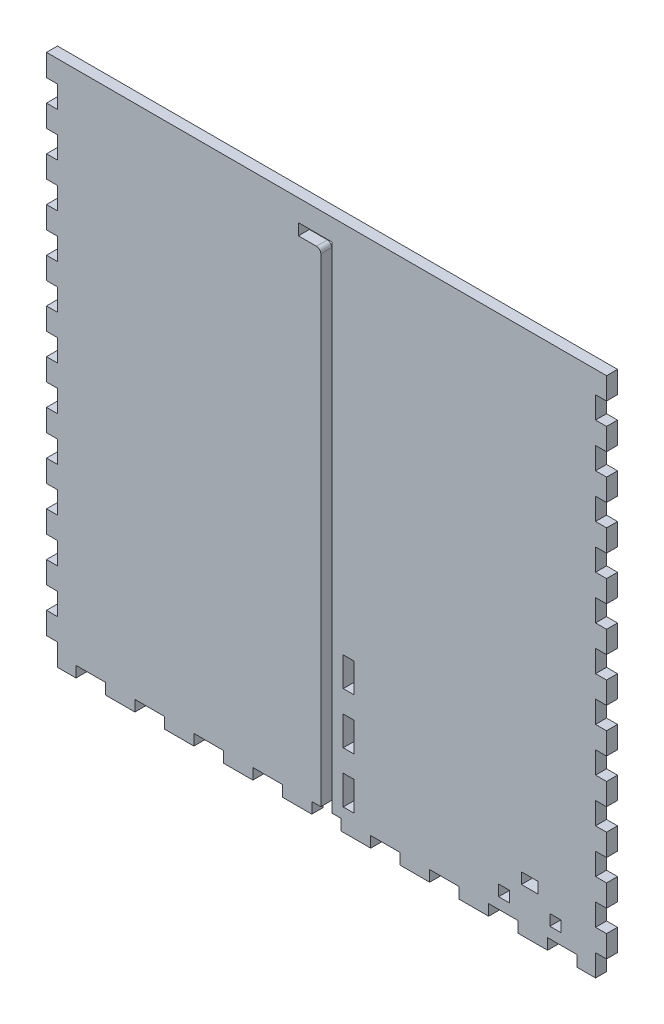
SolidWorks part; units mm, degrees
material "Acrylic (Medium-high impact)"
ref_plane "Front Plane" through (0, 0, 0) normal (0, 0, 1) x (1, 0, 0)
ref_plane "Top Plane" through (0, 0, 0) normal (0, 1, 0) x (1, 0, 0)
ref_plane "Right Plane" through (0, 0, 0) normal (1, 0, 0) x (0, 0, -1)
sketch "Sketch1" plane through (0, 0, 0) normal (0, 1, 0) x (1, 0, 0)
  line L1 (-161.925, 69.85) -> (161.925, 69.85)
  line L2 (-161.925, 69.85) -> (-161.925, -69.85)
  line L3 (-161.925, -69.85) -> (161.925, -69.85)
  line L4 (161.925, 69.85) -> (161.925, -69.85)
  point P4 (-161.925, 0)
  point P6 (0, 69.85)
  dimension "D1" = 139.7
  dimension "D2" = 323.85
extrude "Boss-Extrude1" add sketch "Sketch1" along normal blind 6.35
sketch "Sketch2" plane through (0, 6.35, 0) normal (0, 1, 0) x (1, 0, 0)
  line L0 (161.925, -69.85) -> (161.925, 69.85) construction
  line L1 (-161.925, 69.85) -> (161.925, 69.85)
  line L2 (-161.925, 69.85) -> (-161.925, -69.85)
  line L3 (-161.925, -69.85) -> (161.925, -69.85)
  line L4 (161.925, 69.85) -> (161.925, -69.85)
  line L5 (-161.925, -69.85) -> (161.925, -69.85) construction
  line L7 (-155.575, 63.5) -> (155.575, 63.5)
  line L8 (-155.575, 63.5) -> (-155.575, -63.5)
  line L9 (-155.575, -63.5) -> (155.575, -63.5)
  line L10 (155.575, 63.5) -> (155.575, -63.5)
  point P7 (-155.575, 0)
  point P14 (-161.925, 0)
  point P15 (0, -63.5)
  point P16 (0, -69.85)
  point P17 (155.575, 0)
  point P18 (161.925, 0)
  dimension "D1" = 6.35
  dimension "D2" = 6.35
extrude "Boss-Extrude2" add sketch "Sketch2" along normal blind 298.45
sketch "Sketch3" plane through (0, 0, 69.85) normal (0, 0, 1) x (1, 0, 0)
  line L0 (0, 304.8) -> (0, 0) construction
  line L2 (-155.575, 6.35) -> (155.575, 6.35) construction
  line L4 (-3.302, 283.21) -> (-3.302, 6.35)
  line L5 (-3.302, 6.35) -> (3.302, 6.35)
  line L6 (3.302, 292.354) -> (3.302, 6.35)
  line L7 (3.302, 292.354) -> (-16.256, 292.354)
  line L9 (-5.842, 285.75) -> (-16.256, 285.75)
  line L10 (-16.256, 292.354) -> (-16.256, 285.75)
  line L11 (3.302, 101.6) -> (16.002, 101.6) construction
  line L12 (-161.925, 0) -> (161.925, 0) construction
  line L13 (12.827, 88.9) -> (12.827, 101.6) construction
  line L14 (9.652, 88.9) -> (16.002, 88.9)
  line L15 (9.652, 88.9) -> (9.652, 71.9667)
  line L16 (9.652, 71.9667) -> (16.002, 71.9667)
  line L17 (16.002, 88.9) -> (16.002, 71.9667)
  line L18 (9.652, 42.3333) -> (16.002, 42.3333)
  line L19 (9.652, 42.3333) -> (9.652, 59.2667)
  line L20 (9.652, 59.2667) -> (16.002, 59.2667)
  line L21 (16.002, 42.3333) -> (16.002, 59.2667)
  line L26 (9.652, 29.6333) -> (16.002, 29.6333)
  line L27 (9.652, 29.6333) -> (9.652, 12.7)
  line L28 (9.652, 12.7) -> (16.002, 12.7)
  line L29 (16.002, 29.6333) -> (16.002, 12.7)
  line L30 (12.827, 59.2667) -> (12.827, 71.9667) construction
  line L31 (12.827, 29.6333) -> (12.827, 42.3333) construction
  line L32 (12.827, 12.7) -> (12.827, 0) construction
  line L33 (-161.925, 304.8) -> (161.925, 304.8) construction
  arc A0 (-3.302, 283.21) -> (-5.842, 285.75) centre (-5.842, 283.21) ccw
  point P5 (0, 6.35)
  point P44 (0, 0)
  dimension "D5" = 2.54
  dimension "D1" = 6.604
  dimension "D2" = 12.954
  dimension "D3" = 6.604
  dimension "D4" = 286.004
  dimension "D6" = 101.6
  dimension "D7" = 12.7
  dimension "D8" = 12.7
  dimension "D9" = 6.35
extrude "Door Slot" cut sketch "Sketch3" against normal blind 12.7
sketch "Sketch4" plane through (0, 0, -63.5) normal (0, 0, 1) x (1, 0, 0)
  line L0 (-161.925, 304.8) -> (161.925, 304.8) construction
  line L1 (-22.606, 304.8) -> (-16.256, 304.8)
  line L2 (-22.606, 304.8) -> (-22.606, 6.35)
  line L3 (-22.606, 6.35) -> (-16.256, 6.35)
  line L4 (-16.256, 304.8) -> (-16.256, 6.35)
  line L5 (6.477, 263.525) -> (6.477, 247.65) construction
  line L6 (-16.256, 292.354) -> (-16.256, 285.75) construction
  line L7 (3.302, 304.8) -> (9.652, 304.8)
  line L8 (3.302, 304.8) -> (3.302, 6.35)
  line L9 (3.302, 6.35) -> (9.652, 6.35)
  line L10 (9.652, 304.8) -> (9.652, 6.35)
  line L11 (155.575, 6.35) -> (-155.575, 6.35) construction
  line L12 (3.302, 6.35) -> (3.302, 292.354) construction
  line L13 (-16.256, 304.8) -> (-22.606, 304.8)
  line L14 (-16.256, 304.8) -> (-16.256, 292.1)
  line L15 (-16.256, 292.1) -> (-22.606, 292.1)
  line L16 (-22.606, 304.8) -> (-22.606, 292.1)
  line L17 (-16.256, 276.225) -> (-22.606, 276.225)
  line L18 (-16.256, 276.225) -> (-16.256, 263.525)
  line L19 (-16.256, 263.525) -> (-22.606, 263.525)
  line L20 (-22.606, 276.225) -> (-22.606, 263.525)
  line L21 (-22.606, 6.35) -> (-16.256, 6.35)
  line L22 (-22.606, 6.35) -> (-22.606, 19.05)
  line L23 (-22.606, 19.05) -> (-16.256, 19.05)
  line L24 (-16.256, 6.35) -> (-16.256, 19.05)
  line L25 (-22.606, 34.925) -> (-16.256, 34.925)
  line L26 (-22.606, 34.925) -> (-22.606, 47.625)
  line L27 (-22.606, 47.625) -> (-16.256, 47.625)
  line L28 (-16.256, 34.925) -> (-16.256, 47.625)
  line L29 (-22.606, 92.075) -> (-16.256, 92.075)
  line L30 (-22.606, 92.075) -> (-22.606, 104.775)
  line L31 (-22.606, 104.775) -> (-16.256, 104.775)
  line L32 (-16.256, 92.075) -> (-16.256, 104.775)
  line L33 (-22.606, 149.225) -> (-16.256, 149.225)
  line L34 (-22.606, 149.225) -> (-22.606, 161.925)
  line L35 (-22.606, 161.925) -> (-16.256, 161.925)
  line L36 (-16.256, 149.225) -> (-16.256, 161.925)
  line L37 (-22.606, 177.8) -> (-16.256, 177.8)
  line L38 (-22.606, 177.8) -> (-22.606, 190.5)
  line L39 (-22.606, 190.5) -> (-16.256, 190.5)
  line L40 (-16.256, 177.8) -> (-16.256, 190.5)
  line L41 (-22.606, 206.375) -> (-16.256, 206.375)
  line L42 (-22.606, 206.375) -> (-22.606, 219.075)
  line L43 (-22.606, 219.075) -> (-16.256, 219.075)
  line L44 (-16.256, 206.375) -> (-16.256, 219.075)
  line L45 (-22.606, 234.95) -> (-16.256, 234.95)
  line L46 (-22.606, 234.95) -> (-22.606, 247.65)
  line L47 (-22.606, 247.65) -> (-16.256, 247.65)
  line L48 (-16.256, 234.95) -> (-16.256, 247.65)
  line L49 (-16.256, 133.35) -> (-22.606, 133.35)
  line L50 (-16.256, 133.35) -> (-16.256, 120.65)
  line L51 (-16.256, 120.65) -> (-22.606, 120.65)
  line L52 (-22.606, 133.35) -> (-22.606, 120.65)
  line L53 (-16.256, 76.2) -> (-22.606, 76.2)
  line L54 (-16.256, 76.2) -> (-16.256, 63.5)
  line L55 (-16.256, 63.5) -> (-22.606, 63.5)
  line L56 (-22.606, 76.2) -> (-22.606, 63.5)
  line L57 (-19.431, 304.8) -> (-19.431, 292.1) construction
  line L58 (-19.431, 292.1) -> (-19.431, 276.225) construction
  line L59 (-19.431, 276.225) -> (-19.431, 263.525) construction
  line L60 (-19.431, 247.65) -> (-19.431, 234.95) construction
  line L61 (-19.431, 234.95) -> (-19.431, 219.075) construction
  line L62 (-19.431, 219.075) -> (-19.431, 206.375) construction
  line L63 (-19.431, 206.375) -> (-19.431, 190.5) construction
  line L64 (-19.431, 190.5) -> (-19.431, 177.8) construction
  line L65 (-19.431, 177.8) -> (-19.431, 161.925) construction
  line L66 (-19.431, 161.925) -> (-19.431, 149.225) construction
  line L67 (-19.431, 133.35) -> (-19.431, 120.65) construction
  line L68 (-19.431, 120.65) -> (-19.431, 104.775) construction
  line L69 (-19.431, 104.775) -> (-19.431, 92.075) construction
  line L70 (-19.431, 92.075) -> (-19.431, 76.2) construction
  line L71 (-19.431, 76.2) -> (-19.431, 63.5) construction
  line L72 (-19.431, 63.5) -> (-19.431, 47.625) construction
  line L73 (-19.431, 47.625) -> (-19.431, 34.925) construction
  line L74 (-19.431, 34.925) -> (-19.431, 19.05) construction
  line L75 (-19.431, 19.05) -> (-19.431, 6.35) construction
  line L76 (-19.431, 149.225) -> (-19.431, 133.35) construction
  line L77 (-19.431, 263.525) -> (-19.431, 247.65) construction
  line L78 (-6.477, 304.8) -> (-6.477, 0) construction
  line L79 (161.925, 304.8) -> (-161.925, 304.8) construction
  line L80 (161.925, 0) -> (-161.925, 0) construction
  line L81 (-6.477, 8.3493) -> (3.302, 8.3493) construction
  line L82 (-6.477, 8.3493) -> (-16.256, 8.3493) construction
  line L83 (6.477, 149.225) -> (6.477, 133.35) construction
  line L84 (6.477, 19.05) -> (6.477, 6.35) construction
  line L85 (6.477, 34.925) -> (6.477, 19.05) construction
  line L86 (6.477, 47.625) -> (6.477, 34.925) construction
  line L87 (6.477, 63.5) -> (6.477, 47.625) construction
  line L88 (6.477, 76.2) -> (6.477, 63.5) construction
  line L89 (6.477, 92.075) -> (6.477, 76.2) construction
  line L90 (6.477, 104.775) -> (6.477, 92.075) construction
  line L91 (6.477, 120.65) -> (6.477, 104.775) construction
  line L92 (6.477, 133.35) -> (6.477, 120.65) construction
  line L93 (6.477, 161.925) -> (6.477, 149.225) construction
  line L94 (6.477, 177.8) -> (6.477, 161.925) construction
  line L95 (6.477, 190.5) -> (6.477, 177.8) construction
  line L96 (6.477, 206.375) -> (6.477, 190.5) construction
  line L97 (6.477, 219.075) -> (6.477, 206.375) construction
  line L98 (6.477, 234.95) -> (6.477, 219.075) construction
  line L99 (6.477, 247.65) -> (6.477, 234.95) construction
  line L100 (6.477, 276.225) -> (6.477, 263.525) construction
  line L101 (6.477, 292.1) -> (6.477, 276.225) construction
  line L102 (6.477, 304.8) -> (6.477, 292.1) construction
  line L103 (9.652, 76.2) -> (9.652, 63.5)
  line L104 (3.302, 63.5) -> (9.652, 63.5)
  line L105 (3.302, 76.2) -> (3.302, 63.5)
  line L106 (3.302, 76.2) -> (9.652, 76.2)
  line L107 (9.652, 133.35) -> (9.652, 120.65)
  line L108 (3.302, 120.65) -> (9.652, 120.65)
  line L109 (3.302, 133.35) -> (3.302, 120.65)
  line L110 (3.302, 133.35) -> (9.652, 133.35)
  line L111 (3.302, 234.95) -> (3.302, 247.65)
  line L112 (9.652, 247.65) -> (3.302, 247.65)
  line L113 (9.652, 234.95) -> (9.652, 247.65)
  line L114 (9.652, 234.95) -> (3.302, 234.95)
  line L115 (3.302, 206.375) -> (3.302, 219.075)
  line L116 (9.652, 219.075) -> (3.302, 219.075)
  line L117 (9.652, 206.375) -> (9.652, 219.075)
  line L118 (9.652, 206.375) -> (3.302, 206.375)
  line L119 (3.302, 177.8) -> (3.302, 190.5)
  line L120 (9.652, 190.5) -> (3.302, 190.5)
  line L121 (9.652, 177.8) -> (9.652, 190.5)
  line L122 (9.652, 177.8) -> (3.302, 177.8)
  line L123 (3.302, 149.225) -> (3.302, 161.925)
  line L124 (9.652, 161.925) -> (3.302, 161.925)
  line L125 (9.652, 149.225) -> (9.652, 161.925)
  line L126 (9.652, 149.225) -> (3.302, 149.225)
  line L127 (3.302, 92.075) -> (3.302, 104.775)
  line L128 (9.652, 104.775) -> (3.302, 104.775)
  line L129 (9.652, 92.075) -> (9.652, 104.775)
  line L130 (9.652, 92.075) -> (3.302, 92.075)
  line L131 (3.302, 34.925) -> (3.302, 47.625)
  line L132 (9.652, 47.625) -> (3.302, 47.625)
  line L133 (9.652, 34.925) -> (9.652, 47.625)
  line L134 (9.652, 34.925) -> (3.302, 34.925)
  line L135 (3.302, 6.35) -> (3.302, 19.05)
  line L136 (9.652, 19.05) -> (3.302, 19.05)
  line L137 (9.652, 6.35) -> (9.652, 19.05)
  line L138 (9.652, 6.35) -> (3.302, 6.35)
  line L139 (9.652, 276.225) -> (9.652, 263.525)
  line L140 (3.302, 263.525) -> (9.652, 263.525)
  line L141 (3.302, 276.225) -> (3.302, 263.525)
  line L142 (3.302, 276.225) -> (9.652, 276.225)
  line L143 (9.652, 304.8) -> (9.652, 292.1)
  line L144 (3.302, 292.1) -> (9.652, 292.1)
  line L145 (3.302, 304.8) -> (3.302, 292.1)
  line L146 (3.302, 304.8) -> (9.652, 304.8)
  line L147 (3.302, 304.8) -> (3.302, 6.35)
  line L148 (9.652, 6.35) -> (3.302, 6.35)
  line L149 (9.652, 304.8) -> (9.652, 6.35)
  line L150 (9.652, 304.8) -> (3.302, 304.8)
  point P14 (-16.256, 289.052)
  dimension "D1" = 6.35
  dimension "D2" = 12.7
extrude "Door Guide Holes" cut sketch "Sketch4" against normal up to next (6.35 mm away) contours L17 L4 L15 L2 | L2 L47 L4 L19 | L45 L2 L43 L4 | L41 L2 L39 L4 | L37 L2 L35 L4 | L49 L4 L33 L2 | L4 L51 L2 L31 | L53 L4 L29 L2 | L4 L55 L2 L27 | L25 L2 L23 L4
ref_plane "Plane1" through (-6.477, 0, 0) normal (-1, 0, 0) x (0, 0, 1)
mirror "Mirror1" about plane through (-6.477, 0, 0) normal (-1, 0, 0) of "Door Guide Holes"
sketch "Lever Holes" plane through (0, 0, 69.85) normal (0, 0, 1) x (1, 0, 0)
  line L0 (112.7125, 31.75) -> (122.3645, 31.75)
  line L1 (112.7125, 31.75) -> (112.7125, 25.4)
  line L2 (112.7125, 25.4) -> (122.3645, 25.4)
  line L3 (122.3645, 31.75) -> (122.3645, 25.4)
  line L4 (99.568, 19.05) -> (105.918, 19.05)
  line L5 (99.568, 19.05) -> (99.568, 12.7)
  line L6 (99.568, 12.7) -> (105.918, 12.7)
  line L7 (105.918, 19.05) -> (105.918, 12.7)
  line L8 (129.159, 19.05) -> (135.509, 19.05)
  line L9 (129.159, 19.05) -> (129.159, 12.7)
  line L10 (129.159, 12.7) -> (135.509, 12.7)
  line L11 (135.509, 19.05) -> (135.509, 12.7)
  line L12 (105.918, 15.875) -> (129.159, 15.875) construction
  line L13 (-161.925, 0) -> (161.925, 0) construction
  line L14 (3.302, 6.35) -> (155.575, 6.35) construction
  line L15 (155.575, 6.35) -> (-155.575, 6.35) construction
  point P12 (117.5385, 15.875)
  point P13 (117.5385, 25.4)
  point P14 (104.7589, 25.4)
  point P24 (79.4385, 6.35)
  dimension "D1" = 9.652
  dimension "D2" = 6.35
  dimension "D3" = 6.35
  dimension "D4" = 6.35
  dimension "D5" = 23.241
  dimension "D6" = 25.4
  dimension "D7" = 12.7
  dimension "D8" = 38.1
extrude "Cut-Extrude1" cut sketch "Lever Holes" against normal through all
sketch "Sketch7" plane through (161.925, 0, 0) normal (1, 0, 0) x (0, 0, -1)
  line L0 (-37.211, 92.583) -> (37.211, 92.583)
  line L1 (-37.211, 92.583) -> (-37.211, 18.161)
  line L2 (-37.211, 18.161) -> (37.211, 18.161)
  line L3 (37.211, 92.583) -> (37.211, 18.161)
  line L4 (-69.85, 0) -> (69.85, 0) construction
  circle A0 centre (0, 55.372) radius 26.9875
  circle A1 centre (-37.211, 92.583) radius 3.175
  circle A2 centre (37.211, 92.583) radius 3.175
  circle A3 centre (-37.211, 18.161) radius 3.175
  circle A4 centre (37.211, 18.161) radius 3.175
  point P9 (0, 18.161)
  point P10 (-37.211, 55.372)
  dimension "D3" = 53.975
  dimension "D4" = 6.35
  dimension "D1" = 74.422
  dimension "D2" = 55.372
extrude "Cut-Extrude2" cut sketch "Sketch7" against normal up to next contours A0 | L0 A1 L1 | L1 A1 L0 | L3 A2 L0 | L0 A2 L3 | L2 A3 L1 | L1 A3 L2 | L2 A4 L3 | L3 A4 L2
sketch "Sketch8" plane through (-161.925, 0, 0) normal (-1, 0, 0) x (0, 0, 1)
  line L0 (-69.85, 0) -> (69.85, 0) construction
  circle A0 centre (0, 19.05) radius 3.175
  point P6 (0, 0)
  dimension "D1" = 6.35
  dimension "D2" = 19.05
extrude "Cut-Extrude3" cut sketch "Sketch8" against normal up to next
sketch "Bottom" plane through (0, 0, 0) normal (0, -1, 0) x (1, 0, 0)
  line L0 (-155.575, 63.5) -> (155.575, 63.5) construction
  line L1 (-161.925, 69.85) -> (-144.8803, 69.85)
  line L2 (-161.925, 69.85) -> (-161.925, 63.5)
  line L3 (-161.925, 63.5) -> (-144.8803, 63.5)
  line L4 (-144.8803, 69.85) -> (-144.8803, 63.5)
  line L5 (-144.8803, 69.85) -> (-127.8355, 69.85)
  line L6 (-144.8803, 69.85) -> (-144.8803, 63.5)
  line L7 (-144.8803, 63.5) -> (-127.8355, 63.5)
  line L8 (-127.8355, 69.85) -> (-127.8355, 63.5)
  line L9 (-127.8355, 69.85) -> (-110.7908, 69.85)
  line L10 (-127.8355, 69.85) -> (-127.8355, 63.5)
  line L11 (-127.8355, 63.5) -> (-110.7908, 63.5)
  line L12 (-110.7908, 69.85) -> (-110.7908, 63.5)
  line L13 (-110.7908, 69.85) -> (-93.7461, 69.85)
  line L14 (-110.7908, 69.85) -> (-110.7908, 63.5)
  line L15 (-110.7908, 63.5) -> (-93.7461, 63.5)
  line L16 (-93.7461, 69.85) -> (-93.7461, 63.5)
  line L17 (-161.925, 69.85) -> (161.925, 69.85) construction
  line L18 (-16.256, 63.5) -> (3.302, 63.5) construction
  line L19 (-93.7461, 69.85) -> (-76.7013, 69.85)
  line L20 (-93.7461, 69.85) -> (-93.7461, 63.5)
  line L21 (-93.7461, 63.5) -> (-76.7013, 63.5)
  line L22 (-76.7013, 69.85) -> (-76.7013, 63.5)
  line L23 (-76.7013, 69.85) -> (-59.6566, 69.85)
  line L24 (-76.7013, 69.85) -> (-76.7013, 63.5)
  line L25 (-76.7013, 63.5) -> (-59.6566, 63.5)
  line L26 (-59.6566, 69.85) -> (-59.6566, 63.5)
  line L27 (-59.6566, 69.85) -> (-42.6118, 69.85)
  line L28 (-59.6566, 69.85) -> (-59.6566, 63.5)
  line L29 (-59.6566, 63.5) -> (-42.6118, 63.5)
  line L30 (-42.6118, 69.85) -> (-42.6118, 63.5)
  line L31 (-42.6118, 69.85) -> (-25.5671, 69.85)
  line L32 (-42.6118, 69.85) -> (-42.6118, 63.5)
  line L33 (-42.6118, 63.5) -> (-25.5671, 63.5)
  line L34 (-25.5671, 69.85) -> (-25.5671, 63.5)
  line L36 (-25.5671, 69.85) -> (-8.5224, 69.85)
  line L37 (-25.5671, 69.85) -> (-25.5671, 63.5)
  line L38 (-25.5671, 63.5) -> (-8.5224, 63.5)
  line L39 (-8.5224, 69.85) -> (-8.5224, 63.5)
  line L40 (-8.5224, 69.85) -> (8.5224, 69.85)
  line L41 (-8.5224, 69.85) -> (-8.5224, 63.5)
  line L42 (-8.5224, 63.5) -> (8.5224, 63.5)
  line L43 (8.5224, 69.85) -> (8.5224, 63.5)
  line L44 (8.5224, 69.85) -> (25.5671, 69.85)
  line L45 (8.5224, 69.85) -> (8.5224, 63.5)
  line L46 (8.5224, 63.5) -> (25.5671, 63.5)
  line L47 (25.5671, 69.85) -> (25.5671, 63.5)
  line L48 (25.5671, 69.85) -> (42.6118, 69.85)
  line L49 (25.5671, 69.85) -> (25.5671, 63.5)
  line L50 (25.5671, 63.5) -> (42.6118, 63.5)
  line L51 (42.6118, 69.85) -> (42.6118, 63.5)
  line L52 (42.6118, 69.85) -> (59.6566, 69.85)
  line L53 (42.6118, 69.85) -> (42.6118, 63.5)
  line L54 (42.6118, 63.5) -> (59.6566, 63.5)
  line L55 (59.6566, 69.85) -> (59.6566, 63.5)
  line L56 (59.6566, 69.85) -> (76.7013, 69.85)
  line L57 (59.6566, 69.85) -> (59.6566, 63.5)
  line L58 (59.6566, 63.5) -> (76.7013, 63.5)
  line L59 (76.7013, 69.85) -> (76.7013, 63.5)
  line L60 (76.7013, 69.85) -> (93.7461, 69.85)
  line L61 (76.7013, 69.85) -> (76.7013, 63.5)
  line L62 (76.7013, 63.5) -> (93.7461, 63.5)
  line L63 (93.7461, 69.85) -> (93.7461, 63.5)
  line L64 (93.7461, 69.85) -> (110.7908, 69.85)
  line L65 (93.7461, 69.85) -> (93.7461, 63.5)
  line L66 (93.7461, 63.5) -> (110.7908, 63.5)
  line L67 (110.7908, 69.85) -> (110.7908, 63.5)
  line L68 (110.7908, 69.85) -> (127.8355, 69.85)
  line L69 (110.7908, 69.85) -> (110.7908, 63.5)
  line L70 (110.7908, 63.5) -> (127.8355, 63.5)
  line L71 (127.8355, 69.85) -> (127.8355, 63.5)
  line L72 (127.8355, 69.85) -> (144.8803, 69.85)
  line L73 (127.8355, 69.85) -> (127.8355, 63.5)
  line L74 (127.8355, 63.5) -> (144.8803, 63.5)
  line L75 (144.8803, 69.85) -> (144.8803, 63.5)
  line L76 (-155.575, -63.5) -> (-155.575, 63.5) construction
  line L77 (-161.925, 69.85) -> (-155.575, 69.85)
  line L78 (-161.925, 69.85) -> (-161.925, 57.15)
  line L79 (-161.925, 57.15) -> (-155.575, 57.15)
  line L80 (-155.575, 69.85) -> (-155.575, 57.15)
  line L82 (-161.925, 57.15) -> (-155.575, 57.15)
  line L83 (-161.925, 57.15) -> (-161.925, 44.45)
  line L84 (-161.925, 44.45) -> (-155.575, 44.45)
  line L85 (-155.575, 57.15) -> (-155.575, 44.45)
  line L86 (-161.925, 44.45) -> (-155.575, 44.45)
  line L87 (-161.925, 44.45) -> (-161.925, 31.75)
  line L88 (-161.925, 31.75) -> (-155.575, 31.75)
  line L89 (-155.575, 44.45) -> (-155.575, 31.75)
  line L90 (-161.925, 31.75) -> (-155.575, 31.75)
  line L91 (-161.925, 31.75) -> (-161.925, 19.05)
  line L92 (-161.925, 19.05) -> (-155.575, 19.05)
  line L93 (-155.575, 31.75) -> (-155.575, 19.05)
  line L94 (-161.925, 19.05) -> (-155.575, 19.05)
  line L95 (-161.925, 19.05) -> (-161.925, 6.35)
  line L96 (-161.925, 6.35) -> (-155.575, 6.35)
  line L97 (-155.575, 19.05) -> (-155.575, 6.35)
  line L98 (-161.925, 6.35) -> (-155.575, 6.35)
  line L99 (-161.925, 6.35) -> (-161.925, -6.35)
  line L100 (-161.925, -6.35) -> (-155.575, -6.35)
  line L101 (-155.575, 6.35) -> (-155.575, -6.35)
  line L102 (-161.925, -6.35) -> (-155.575, -6.35)
  line L103 (-161.925, -6.35) -> (-161.925, -19.05)
  line L104 (-161.925, -19.05) -> (-155.575, -19.05)
  line L105 (-155.575, -6.35) -> (-155.575, -19.05)
  line L106 (-161.925, -19.05) -> (-155.575, -19.05)
  line L107 (-161.925, -19.05) -> (-161.925, -31.75)
  line L108 (-161.925, -31.75) -> (-155.575, -31.75)
  line L109 (-155.575, -19.05) -> (-155.575, -31.75)
  line L110 (-161.925, -31.75) -> (-155.575, -31.75)
  line L111 (-161.925, -31.75) -> (-161.925, -44.45)
  line L112 (-161.925, -44.45) -> (-155.575, -44.45)
  line L113 (-155.575, -31.75) -> (-155.575, -44.45)
  line L114 (-161.925, -44.45) -> (-155.575, -44.45)
  line L115 (-161.925, -44.45) -> (-161.925, -57.15)
  line L116 (-161.925, -57.15) -> (-155.575, -57.15)
  line L117 (-155.575, -44.45) -> (-155.575, -57.15)
  line L118 (161.925, 69.85) -> (161.925, -69.85) construction
  line L119 (144.8803, 69.85) -> (161.925, 69.85)
  line L120 (144.8803, 69.85) -> (144.8803, 63.5)
  line L121 (144.8803, 63.5) -> (161.925, 63.5)
  line L122 (161.925, 69.85) -> (161.925, 63.5)
  line L123 (161.925, -69.85) -> (-161.925, -69.85) construction
  line L124 (-161.925, -57.15) -> (-155.575, -57.15)
  line L125 (-161.925, -57.15) -> (-161.925, -69.85)
  line L126 (-161.925, -69.85) -> (-155.575, -69.85)
  line L127 (-155.575, -57.15) -> (-155.575, -69.85)
  line L128 (167.64, 0) -> (-167.64, 0) construction
  line L129 (161.925, -69.85) -> (161.925, -63.5)
  line L130 (144.8803, -63.5) -> (161.925, -63.5)
  line L131 (144.8803, -69.85) -> (161.925, -69.85)
  line L132 (144.8803, -69.85) -> (144.8803, -63.5)
  line L133 (127.8355, -63.5) -> (144.8803, -63.5)
  line L134 (127.8355, -69.85) -> (144.8803, -69.85)
  line L135 (127.8355, -69.85) -> (127.8355, -63.5)
  line L136 (110.7908, -63.5) -> (127.8355, -63.5)
  line L137 (110.7908, -69.85) -> (127.8355, -69.85)
  line L138 (110.7908, -69.85) -> (110.7908, -63.5)
  line L139 (93.7461, -63.5) -> (110.7908, -63.5)
  line L140 (93.7461, -69.85) -> (110.7908, -69.85)
  line L141 (93.7461, -69.85) -> (93.7461, -63.5)
  line L142 (76.7013, -63.5) -> (93.7461, -63.5)
  line L143 (76.7013, -69.85) -> (93.7461, -69.85)
  line L144 (59.6566, -63.5) -> (76.7013, -63.5)
  line L145 (76.7013, -69.85) -> (76.7013, -63.5)
  line L146 (59.6566, -69.85) -> (76.7013, -69.85)
  line L147 (59.6566, -69.85) -> (59.6566, -63.5)
  line L148 (42.6118, -63.5) -> (59.6566, -63.5)
  line L149 (42.6118, -69.85) -> (59.6566, -69.85)
  line L150 (42.6118, -69.85) -> (42.6118, -63.5)
  line L151 (25.5671, -63.5) -> (42.6118, -63.5)
  line L152 (25.5671, -69.85) -> (42.6118, -69.85)
  line L153 (25.5671, -69.85) -> (25.5671, -63.5)
  line L154 (8.5224, -69.85) -> (25.5671, -69.85)
  line L155 (8.5224, -63.5) -> (25.5671, -63.5)
  line L156 (8.5224, -69.85) -> (8.5224, -63.5)
  line L157 (-8.5224, -63.5) -> (8.5224, -63.5)
  line L158 (-8.5224, -69.85) -> (8.5224, -69.85)
  line L159 (-25.5671, -63.5) -> (-8.5224, -63.5)
  line L160 (-8.5224, -69.85) -> (-8.5224, -63.5)
  line L161 (-25.5671, -69.85) -> (-8.5224, -69.85)
  line L162 (-25.5671, -69.85) -> (-25.5671, -63.5)
  line L163 (-42.6118, -63.5) -> (-25.5671, -63.5)
  line L164 (-42.6118, -69.85) -> (-25.5671, -69.85)
  line L165 (-42.6118, -69.85) -> (-42.6118, -63.5)
  line L166 (-59.6566, -63.5) -> (-42.6118, -63.5)
  line L167 (-59.6566, -69.85) -> (-42.6118, -69.85)
  line L168 (-59.6566, -69.85) -> (-59.6566, -63.5)
  line L169 (-76.7013, -69.85) -> (-59.6566, -69.85)
  line L170 (-76.7013, -63.5) -> (-59.6566, -63.5)
  line L171 (-93.7461, -63.5) -> (-76.7013, -63.5)
  line L172 (-76.7013, -69.85) -> (-76.7013, -63.5)
  line L173 (-93.7461, -69.85) -> (-76.7013, -69.85)
  line L174 (-110.7908, -69.85) -> (-93.7461, -69.85)
  line L175 (-110.7908, -63.5) -> (-93.7461, -63.5)
  line L176 (-93.7461, -69.85) -> (-93.7461, -63.5)
  line L177 (-127.8355, -69.85) -> (-127.8355, -63.5)
  line L178 (-127.8355, -69.85) -> (-110.7908, -69.85)
  line L179 (-110.7908, -69.85) -> (-110.7908, -63.5)
  line L180 (-127.8355, -63.5) -> (-110.7908, -63.5)
  line L181 (-144.8803, -63.5) -> (-127.8355, -63.5)
  line L182 (-144.8803, -69.85) -> (-127.8355, -69.85)
  line L183 (-144.8803, -69.85) -> (-144.8803, -63.5)
  line L184 (-161.925, -69.85) -> (-144.8803, -69.85)
  line L185 (-161.925, -69.85) -> (-161.925, -63.5)
  line L186 (-161.925, -63.5) -> (-144.8803, -63.5)
  line L187 (0, -76.835) -> (0, 76.835) construction
  line L188 (161.925, -69.85) -> (155.575, -69.85)
  line L189 (155.575, -57.15) -> (155.575, -69.85)
  line L190 (161.925, -57.15) -> (161.925, -69.85)
  line L191 (161.925, -57.15) -> (155.575, -57.15)
  line L192 (155.575, -44.45) -> (155.575, -57.15)
  line L193 (161.925, -44.45) -> (161.925, -57.15)
  line L194 (161.925, -44.45) -> (155.575, -44.45)
  line L195 (155.575, -31.75) -> (155.575, -44.45)
  line L196 (161.925, -31.75) -> (161.925, -44.45)
  line L197 (161.925, -31.75) -> (155.575, -31.75)
  line L198 (161.925, -19.05) -> (161.925, -31.75)
  line L199 (155.575, -19.05) -> (155.575, -31.75)
  line L200 (155.575, -6.35) -> (155.575, -19.05)
  line L201 (161.925, -6.35) -> (161.925, -19.05)
  line L202 (161.925, -19.05) -> (155.575, -19.05)
  line L203 (161.925, -6.35) -> (155.575, -6.35)
  line L204 (155.575, 6.35) -> (155.575, -6.35)
  line L205 (161.925, 6.35) -> (161.925, -6.35)
  line L206 (161.925, 6.35) -> (155.575, 6.35)
  line L207 (155.575, 19.05) -> (155.575, 6.35)
  line L208 (161.925, 19.05) -> (161.925, 6.35)
  line L209 (161.925, 19.05) -> (155.575, 19.05)
  line L210 (161.925, 31.75) -> (155.575, 31.75)
  line L211 (161.925, 44.45) -> (155.575, 44.45)
  line L212 (161.925, 57.15) -> (155.575, 57.15)
  line L213 (155.575, 31.75) -> (155.575, 19.05)
  line L214 (161.925, 31.75) -> (161.925, 19.05)
  line L215 (155.575, 44.45) -> (155.575, 31.75)
  line L216 (161.925, 44.45) -> (161.925, 31.75)
  line L217 (155.575, 57.15) -> (155.575, 44.45)
  line L218 (161.925, 57.15) -> (161.925, 44.45)
  line L219 (155.575, 69.85) -> (155.575, 57.15)
  line L220 (161.925, 69.85) -> (161.925, 57.15)
sketch "Front/Back" plane through (0, 0, 69.85) normal (0, 0, 1) x (1, 0, 0)
  line L0 (-155.575, 6.35) -> (-3.302, 6.35) construction
  line L1 (-161.925, 0) -> (-144.8803, 0)
  line L2 (-161.925, 0) -> (-161.925, 6.35)
  line L3 (-161.925, 6.35) -> (-144.8803, 6.35)
  line L4 (-144.8803, 0) -> (-144.8803, 6.35)
  line L5 (-161.925, 0) -> (161.925, 0) construction
  line L6 (-127.8355, 0) -> (-110.7908, 0) construction
  line L7 (-144.8803, 6.35) -> (-127.8355, 6.35)
  line L8 (-144.8803, 6.35) -> (-144.8803, 0)
  line L9 (-144.8803, 0) -> (-127.8355, 0)
  line L10 (-127.8355, 6.35) -> (-127.8355, 0)
  line L11 (-93.7461, 0) -> (-76.7013, 0) construction
  line L12 (-127.8355, 6.35) -> (-110.7908, 6.35)
  line L13 (-127.8355, 6.35) -> (-127.8355, 0)
  line L14 (-127.8355, 0) -> (-110.7908, 0)
  line L15 (-110.7908, 6.35) -> (-110.7908, 0)
  line L16 (-110.7908, 6.35) -> (-93.7461, 6.35)
  line L17 (-110.7908, 6.35) -> (-110.7908, 0)
  line L18 (-110.7908, 0) -> (-93.7461, 0)
  line L19 (-93.7461, 6.35) -> (-93.7461, 0)
  line L20 (-76.7013, 0) -> (-59.6566, 0) construction
  line L21 (-93.7461, 6.35) -> (-76.7013, 6.35)
  line L22 (-93.7461, 6.35) -> (-93.7461, 0)
  line L23 (-93.7461, 0) -> (-76.7013, 0)
  line L24 (-76.7013, 6.35) -> (-76.7013, 0)
  line L25 (-76.7013, 6.35) -> (-59.6566, 6.35)
  line L26 (-76.7013, 6.35) -> (-76.7013, 0)
  line L27 (-76.7013, 0) -> (-59.6566, 0)
  line L28 (-59.6566, 6.35) -> (-59.6566, 0)
  line L29 (-59.6566, 0) -> (-42.6118, 0) construction
  line L30 (-59.6566, 6.35) -> (-42.6118, 6.35)
  line L31 (-59.6566, 6.35) -> (-59.6566, 0)
  line L32 (-59.6566, 0) -> (-42.6118, 0)
  line L33 (-42.6118, 6.35) -> (-42.6118, 0)
  line L34 (-25.5671, 0) -> (-8.5224, 0) construction
  line L35 (-42.6118, 6.35) -> (-25.5671, 6.35)
  line L36 (-42.6118, 6.35) -> (-42.6118, 0)
  line L37 (-42.6118, 0) -> (-25.5671, 0)
  line L38 (-25.5671, 6.35) -> (-25.5671, 0)
  line L39 (8.5224, 0) -> (25.5671, 0) construction
  line L40 (-25.5671, 6.35) -> (-8.5224, 6.35)
  line L41 (-25.5671, 6.35) -> (-25.5671, 0)
  line L42 (-25.5671, 0) -> (-8.5224, 0)
  line L43 (-8.5224, 6.35) -> (-8.5224, 0)
  line L44 (-8.5224, 6.35) -> (8.5224, 6.35)
  line L45 (-8.5224, 6.35) -> (-8.5224, 0)
  line L46 (-8.5224, 0) -> (8.5224, 0)
  line L47 (8.5224, 6.35) -> (8.5224, 0)
  line L48 (8.5224, 0) -> (25.5671, 0) construction
  line L49 (42.6118, 0) -> (59.6566, 0) construction
  line L50 (8.5224, 6.35) -> (25.5671, 6.35)
  line L51 (8.5224, 6.35) -> (8.5224, 0)
  line L52 (8.5224, 0) -> (25.5671, 0)
  line L53 (25.5671, 6.35) -> (25.5671, 0)
  line L54 (25.5671, 6.35) -> (42.6118, 6.35)
  line L55 (25.5671, 6.35) -> (25.5671, 0)
  line L56 (25.5671, 0) -> (42.6118, 0)
  line L57 (42.6118, 6.35) -> (42.6118, 0)
  line L58 (76.7013, 0) -> (93.7461, 0) construction
  line L59 (42.6118, 6.35) -> (59.6566, 6.35)
  line L60 (42.6118, 6.35) -> (42.6118, 0)
  line L61 (42.6118, 0) -> (59.6566, 0)
  line L62 (59.6566, 6.35) -> (59.6566, 0)
  line L63 (59.6566, 6.35) -> (76.7013, 6.35)
  line L64 (59.6566, 6.35) -> (59.6566, 0)
  line L65 (59.6566, 0) -> (76.7013, 0)
  line L66 (76.7013, 6.35) -> (76.7013, 0)
  line L67 (59.6566, 0) -> (76.7013, 0) construction
  line L68 (110.7908, 0) -> (127.8355, 0) construction
  line L69 (76.7013, 6.35) -> (93.7461, 6.35)
  line L70 (76.7013, 6.35) -> (76.7013, 0)
  line L71 (76.7013, 0) -> (93.7461, 0)
  line L72 (93.7461, 6.35) -> (93.7461, 0)
  line L73 (93.7461, 6.35) -> (110.7908, 6.35)
  line L74 (93.7461, 6.35) -> (93.7461, 0)
  line L75 (93.7461, 0) -> (110.7908, 0)
  line L76 (110.7908, 6.35) -> (110.7908, 0)
  line L77 (127.8355, 0) -> (144.8803, 0) construction
  line L78 (110.7908, 6.35) -> (127.8355, 6.35)
  line L79 (110.7908, 6.35) -> (110.7908, 0)
  line L80 (110.7908, 0) -> (127.8355, 0)
  line L81 (127.8355, 6.35) -> (127.8355, 0)
  line L82 (127.8355, 0) -> (144.8803, 0) construction
  line L84 (127.8355, 6.35) -> (144.8803, 6.35)
  line L85 (127.8355, 6.35) -> (127.8355, 0)
  line L86 (127.8355, 0) -> (144.8803, 0)
  line L87 (144.8803, 6.35) -> (144.8803, 0)
  line L88 (144.8803, 6.35) -> (161.925, 6.35)
  line L89 (144.8803, 6.35) -> (144.8803, 0)
  line L90 (144.8803, 0) -> (161.925, 0)
  line L91 (161.925, 6.35) -> (161.925, 0)
  line L92 (-155.575, 304.8) -> (-155.575, 6.35) construction
  line L93 (-161.925, 0) -> (-155.575, 0)
  line L94 (-161.925, 0) -> (-161.925, 12.7)
  line L95 (-161.925, 12.7) -> (-155.575, 12.7)
  line L96 (-155.575, 0) -> (-155.575, 12.7)
  line L97 (-161.925, 304.8) -> (-161.925, 0) construction
  line L98 (-161.925, 12.7) -> (-155.575, 12.7)
  line L99 (-161.925, 12.7) -> (-161.925, 25.4)
  line L100 (-161.925, 25.4) -> (-155.575, 25.4)
  line L101 (-155.575, 12.7) -> (-155.575, 25.4)
  line L102 (-161.925, 25.4) -> (-155.575, 25.4)
  line L103 (-161.925, 25.4) -> (-161.925, 38.1)
  line L104 (-161.925, 38.1) -> (-155.575, 38.1)
  line L105 (-155.575, 25.4) -> (-155.575, 38.1)
  line L106 (-161.925, 38.1) -> (-155.575, 38.1)
  line L107 (-161.925, 38.1) -> (-161.925, 50.8)
  line L108 (-161.925, 50.8) -> (-155.575, 50.8)
  line L109 (-155.575, 38.1) -> (-155.575, 50.8)
  line L110 (-161.925, 50.8) -> (-155.575, 50.8)
  line L111 (-161.925, 50.8) -> (-161.925, 63.5)
  line L112 (-161.925, 63.5) -> (-155.575, 63.5)
  line L113 (-155.575, 50.8) -> (-155.575, 63.5)
  line L114 (-161.925, 63.5) -> (-155.575, 63.5)
  line L115 (-161.925, 63.5) -> (-161.925, 76.2)
  line L116 (-161.925, 76.2) -> (-155.575, 76.2)
  line L117 (-155.575, 63.5) -> (-155.575, 76.2)
  line L118 (-161.925, 76.2) -> (-155.575, 76.2)
  line L119 (-161.925, 76.2) -> (-161.925, 88.9)
  line L120 (-161.925, 88.9) -> (-155.575, 88.9)
  line L121 (-155.575, 76.2) -> (-155.575, 88.9)
  line L122 (-161.925, 88.9) -> (-155.575, 88.9)
  line L123 (-161.925, 88.9) -> (-161.925, 101.6)
  line L124 (-161.925, 101.6) -> (-155.575, 101.6)
  line L125 (-155.575, 88.9) -> (-155.575, 101.6)
  line L126 (-161.925, 101.6) -> (-155.575, 101.6)
  line L127 (-161.925, 101.6) -> (-161.925, 114.3)
  line L128 (-161.925, 114.3) -> (-155.575, 114.3)
  line L129 (-155.575, 101.6) -> (-155.575, 114.3)
  line L130 (-161.925, 114.3) -> (-155.575, 114.3)
  line L131 (-161.925, 114.3) -> (-161.925, 127)
  line L132 (-161.925, 127) -> (-155.575, 127)
  line L133 (-155.575, 114.3) -> (-155.575, 127)
  line L134 (-161.925, 127) -> (-155.575, 127)
  line L135 (-161.925, 127) -> (-161.925, 139.7)
  line L136 (-161.925, 139.7) -> (-155.575, 139.7)
  line L137 (-155.575, 127) -> (-155.575, 139.7)
  line L138 (-161.925, 139.7) -> (-155.575, 139.7)
  line L139 (-161.925, 139.7) -> (-161.925, 152.4)
  line L140 (-161.925, 152.4) -> (-155.575, 152.4)
  line L141 (-155.575, 139.7) -> (-155.575, 152.4)
  line L142 (-161.925, 152.4) -> (-155.575, 152.4)
  line L143 (-161.925, 152.4) -> (-161.925, 165.1)
  line L144 (-161.925, 165.1) -> (-155.575, 165.1)
  line L145 (-155.575, 152.4) -> (-155.575, 165.1)
  line L146 (-161.925, 165.1) -> (-155.575, 165.1)
  line L147 (-161.925, 165.1) -> (-161.925, 177.8)
  line L148 (-161.925, 177.8) -> (-155.575, 177.8)
  line L149 (-155.575, 165.1) -> (-155.575, 177.8)
  line L150 (-161.925, 177.8) -> (-155.575, 177.8)
  line L151 (-161.925, 177.8) -> (-161.925, 190.5)
  line L152 (-161.925, 190.5) -> (-155.575, 190.5)
  line L153 (-155.575, 177.8) -> (-155.575, 190.5)
  line L154 (-161.925, 190.5) -> (-155.575, 190.5)
  line L155 (-161.925, 190.5) -> (-161.925, 203.2)
  line L156 (-161.925, 203.2) -> (-155.575, 203.2)
  line L157 (-155.575, 190.5) -> (-155.575, 203.2)
  line L158 (-161.925, 203.2) -> (-155.575, 203.2)
  line L159 (-161.925, 203.2) -> (-161.925, 215.9)
  line L160 (-161.925, 215.9) -> (-155.575, 215.9)
  line L161 (-155.575, 203.2) -> (-155.575, 215.9)
  line L162 (-161.925, 215.9) -> (-155.575, 215.9)
  line L163 (-161.925, 215.9) -> (-161.925, 228.6)
  line L164 (-161.925, 228.6) -> (-155.575, 228.6)
  line L165 (-155.575, 215.9) -> (-155.575, 228.6)
  line L166 (-161.925, 228.6) -> (-155.575, 228.6)
  line L167 (-161.925, 228.6) -> (-161.925, 241.3)
  line L168 (-161.925, 241.3) -> (-155.575, 241.3)
  line L169 (-155.575, 228.6) -> (-155.575, 241.3)
  line L170 (-161.925, 241.3) -> (-155.575, 241.3)
  line L171 (-161.925, 241.3) -> (-161.925, 254)
  line L172 (-161.925, 254) -> (-155.575, 254)
  line L173 (-155.575, 241.3) -> (-155.575, 254)
  line L174 (-161.925, 254) -> (-155.575, 254)
  line L175 (-161.925, 254) -> (-161.925, 266.7)
  line L176 (-161.925, 266.7) -> (-155.575, 266.7)
  line L177 (-155.575, 254) -> (-155.575, 266.7)
  line L178 (-161.925, 266.7) -> (-155.575, 266.7)
  line L179 (-161.925, 266.7) -> (-161.925, 279.4)
  line L180 (-161.925, 279.4) -> (-155.575, 279.4)
  line L181 (-155.575, 266.7) -> (-155.575, 279.4)
  line L182 (-161.925, 279.4) -> (-155.575, 279.4)
  line L183 (-161.925, 279.4) -> (-161.925, 292.1)
  line L184 (-161.925, 292.1) -> (-155.575, 292.1)
  line L185 (-155.575, 279.4) -> (-155.575, 292.1)
  line L186 (-161.925, 292.1) -> (-155.575, 292.1)
  line L187 (-161.925, 292.1) -> (-161.925, 304.8)
  line L188 (-161.925, 304.8) -> (-155.575, 304.8)
  line L189 (-155.575, 292.1) -> (-155.575, 304.8)
  line L190 (-161.925, 304.8) -> (-155.575, 304.8)
  line L194 (-161.925, 304.8) -> (161.925, 304.8) construction
  line L195 (0, -76.835) -> (0, 76.835) construction
  line L196 (161.925, 304.8) -> (155.575, 304.8)
  line L197 (155.575, 292.1) -> (155.575, 304.8)
  line L198 (161.925, 304.8) -> (155.575, 304.8)
  line L199 (161.925, 292.1) -> (161.925, 304.8)
  line L200 (161.925, 292.1) -> (155.575, 292.1)
  line L201 (155.575, 279.4) -> (155.575, 292.1)
  line L202 (161.925, 292.1) -> (155.575, 292.1)
  line L203 (161.925, 279.4) -> (161.925, 292.1)
  line L204 (161.925, 279.4) -> (155.575, 279.4)
  line L205 (155.575, 266.7) -> (155.575, 279.4)
  line L206 (161.925, 279.4) -> (155.575, 279.4)
  line L207 (161.925, 266.7) -> (161.925, 279.4)
  line L208 (161.925, 266.7) -> (155.575, 266.7)
  line L209 (155.575, 254) -> (155.575, 266.7)
  line L210 (161.925, 266.7) -> (155.575, 266.7)
  line L211 (161.925, 254) -> (161.925, 266.7)
  line L212 (161.925, 254) -> (155.575, 254)
  line L213 (155.575, 241.3) -> (155.575, 254)
  line L214 (161.925, 254) -> (155.575, 254)
  line L215 (161.925, 241.3) -> (161.925, 254)
  line L216 (161.925, 241.3) -> (155.575, 241.3)
  line L217 (155.575, 228.6) -> (155.575, 241.3)
  line L218 (161.925, 241.3) -> (155.575, 241.3)
  line L219 (161.925, 228.6) -> (161.925, 241.3)
  line L220 (161.925, 228.6) -> (155.575, 228.6)
  line L221 (155.575, 215.9) -> (155.575, 228.6)
  line L222 (161.925, 228.6) -> (155.575, 228.6)
  line L223 (161.925, 215.9) -> (161.925, 228.6)
  line L224 (161.925, 215.9) -> (155.575, 215.9)
  line L225 (155.575, 203.2) -> (155.575, 215.9)
  line L226 (161.925, 215.9) -> (155.575, 215.9)
  line L227 (161.925, 203.2) -> (161.925, 215.9)
  line L228 (161.925, 203.2) -> (155.575, 203.2)
  line L229 (155.575, 190.5) -> (155.575, 203.2)
  line L230 (161.925, 203.2) -> (155.575, 203.2)
  line L231 (161.925, 190.5) -> (161.925, 203.2)
  line L232 (161.925, 190.5) -> (155.575, 190.5)
  line L233 (155.575, 177.8) -> (155.575, 190.5)
  line L234 (161.925, 190.5) -> (155.575, 190.5)
  line L235 (161.925, 177.8) -> (161.925, 190.5)
  line L236 (161.925, 177.8) -> (155.575, 177.8)
  line L237 (155.575, 165.1) -> (155.575, 177.8)
  line L238 (161.925, 177.8) -> (155.575, 177.8)
  line L239 (161.925, 165.1) -> (161.925, 177.8)
  line L240 (161.925, 165.1) -> (155.575, 165.1)
  line L241 (155.575, 152.4) -> (155.575, 165.1)
  line L242 (161.925, 165.1) -> (155.575, 165.1)
  line L243 (161.925, 152.4) -> (161.925, 165.1)
  line L244 (161.925, 152.4) -> (155.575, 152.4)
  line L245 (155.575, 139.7) -> (155.575, 152.4)
  line L246 (161.925, 152.4) -> (155.575, 152.4)
  line L247 (161.925, 139.7) -> (161.925, 152.4)
  line L248 (161.925, 139.7) -> (155.575, 139.7)
  line L249 (155.575, 127) -> (155.575, 139.7)
  line L250 (161.925, 139.7) -> (155.575, 139.7)
  line L251 (161.925, 127) -> (161.925, 139.7)
  line L252 (161.925, 127) -> (155.575, 127)
  line L253 (155.575, 114.3) -> (155.575, 127)
  line L254 (161.925, 127) -> (155.575, 127)
  line L255 (161.925, 114.3) -> (161.925, 127)
  line L256 (161.925, 114.3) -> (155.575, 114.3)
  line L257 (155.575, 101.6) -> (155.575, 114.3)
  line L258 (161.925, 114.3) -> (155.575, 114.3)
  line L259 (161.925, 101.6) -> (161.925, 114.3)
  line L260 (161.925, 101.6) -> (155.575, 101.6)
  line L261 (155.575, 88.9) -> (155.575, 101.6)
  line L262 (161.925, 101.6) -> (155.575, 101.6)
  line L263 (161.925, 88.9) -> (161.925, 101.6)
  line L264 (161.925, 88.9) -> (155.575, 88.9)
  line L265 (155.575, 76.2) -> (155.575, 88.9)
  line L266 (161.925, 88.9) -> (155.575, 88.9)
  line L267 (161.925, 76.2) -> (161.925, 88.9)
  line L268 (161.925, 76.2) -> (155.575, 76.2)
  line L269 (155.575, 63.5) -> (155.575, 76.2)
  line L270 (161.925, 76.2) -> (155.575, 76.2)
  line L271 (161.925, 63.5) -> (161.925, 76.2)
  line L272 (161.925, 63.5) -> (155.575, 63.5)
  line L273 (155.575, 50.8) -> (155.575, 63.5)
  line L274 (161.925, 63.5) -> (155.575, 63.5)
  line L275 (161.925, 50.8) -> (161.925, 63.5)
  line L276 (161.925, 50.8) -> (155.575, 50.8)
  line L277 (155.575, 38.1) -> (155.575, 50.8)
  line L278 (161.925, 50.8) -> (155.575, 50.8)
  line L279 (161.925, 38.1) -> (161.925, 50.8)
  line L280 (161.925, 38.1) -> (155.575, 38.1)
  line L281 (155.575, 25.4) -> (155.575, 38.1)
  line L282 (161.925, 38.1) -> (155.575, 38.1)
  line L283 (161.925, 25.4) -> (161.925, 38.1)
  line L284 (161.925, 25.4) -> (155.575, 25.4)
  line L285 (155.575, 12.7) -> (155.575, 25.4)
  line L286 (161.925, 25.4) -> (155.575, 25.4)
  line L287 (161.925, 12.7) -> (161.925, 25.4)
  line L288 (161.925, 12.7) -> (155.575, 12.7)
  line L289 (155.575, 0) -> (155.575, 12.7)
  line L290 (161.925, 12.7) -> (155.575, 12.7)
  line L291 (161.925, 0) -> (161.925, 12.7)
  line L292 (161.925, 0) -> (155.575, 0)
  line L293 (161.925, 0) -> (161.925, 6.35)
  line M74 (3.302, 6.35) -> (-3.302, 6.35)
  line M91 (-161.925, 0) -> (161.925, 0)
  line M92 (161.925, 0) -> (161.925, 304.8)
  line M94 (-161.925, 304.8) -> (-161.925, 0)
sketch "Left/Right" plane through (-161.925, 0, 0) normal (-1, 0, 0) x (0, 0, 1)
  line L0 (57.15, 0) -> (44.45, 0) construction
  line L8 (57.15, 0) -> (57.15, 6.35)
  line L9 (57.15, 6.35) -> (44.45, 6.35)
  line L10 (57.15, 6.35) -> (57.15, 0)
  line L11 (57.15, 0) -> (44.45, 0)
  line L12 (44.45, 6.35) -> (44.45, 0)
  line L13 (-69.85, 0) -> (69.85, 0) construction
  line L14 (44.45, 0) -> (31.75, 0) construction
  line L15 (44.45, 6.35) -> (31.75, 6.35)
  line L16 (44.45, 6.35) -> (44.45, 0)
  line L17 (44.45, 0) -> (31.75, 0)
  line L18 (31.75, 6.35) -> (31.75, 0)
  line L19 (31.75, 0) -> (19.05, 0) construction
  line L20 (31.75, 6.35) -> (19.05, 6.35)
  line L21 (31.75, 6.35) -> (31.75, 0)
  line L22 (31.75, 0) -> (19.05, 0)
  line L23 (19.05, 6.35) -> (19.05, 0)
  line L24 (19.05, 0) -> (6.35, 0) construction
  line L25 (19.05, 6.35) -> (6.35, 6.35)
  line L26 (19.05, 6.35) -> (19.05, 0)
  line L27 (19.05, 0) -> (6.35, 0)
  line L28 (6.35, 6.35) -> (6.35, 0)
  line L29 (6.35, 0) -> (-6.35, 0) construction
  line L30 (6.35, 6.35) -> (-6.35, 6.35)
  line L31 (6.35, 6.35) -> (6.35, 0)
  line L32 (6.35, 0) -> (-6.35, 0)
  line L33 (-6.35, 6.35) -> (-6.35, 0)
  line L34 (-6.35, 0) -> (-19.05, 0) construction
  line L35 (-6.35, 6.35) -> (-19.05, 6.35)
  line L36 (-6.35, 6.35) -> (-6.35, 0)
  line L37 (-6.35, 0) -> (-19.05, 0)
  line L38 (-19.05, 6.35) -> (-19.05, 0)
  line L39 (-19.05, 0) -> (-31.75, 0) construction
  line L40 (-19.05, 6.35) -> (-31.75, 6.35)
  line L41 (-19.05, 6.35) -> (-19.05, 0)
  line L42 (-19.05, 0) -> (-31.75, 0)
  line L43 (-31.75, 6.35) -> (-31.75, 0)
  line L44 (-19.05, 0) -> (-31.75, 0) construction
  line L45 (-31.75, 0) -> (-44.45, 0) construction
  line L46 (-31.75, 6.35) -> (-44.45, 6.35)
  line L47 (-31.75, 6.35) -> (-31.75, 0)
  line L48 (-31.75, 0) -> (-44.45, 0)
  line L49 (-44.45, 6.35) -> (-44.45, 0)
  line L50 (69.85, 304.8) -> (69.85, 0) construction
  line L51 (-44.45, 6.35) -> (-57.15, 6.35)
  line L52 (-44.45, 6.35) -> (-44.45, 0)
  line L53 (-44.45, 0) -> (-57.15, 0)
  line L55 (-69.85, 0) -> (-63.5, 0) construction
  line L57 (-57.15, 6.35) -> (-57.15, 0)
  line L60 (-69.85, 0) -> (-63.5, 0) construction
  line L61 (69.85, 0) -> (57.15, 0) construction
  line L63 (-69.85, 6.35) -> (-69.85, 0)
  line L65 (57.15, 6.35) -> (69.85, 6.35)
  line L66 (57.15, 6.35) -> (57.15, 0)
  line L67 (57.15, 0) -> (69.85, 0)
  line L68 (69.85, 6.35) -> (69.85, 0)
  line L69 (69.85, 165.1) -> (69.85, 177.8) construction
  line L70 (63.5, 12.7) -> (69.85, 12.7)
  line L71 (63.5, 12.7) -> (63.5, 25.4)
  line L72 (63.5, 25.4) -> (69.85, 25.4)
  line L73 (-57.15, 0) -> (-69.85, 0)
  line L74 (-69.85, 6.35) -> (-57.15, 6.35)
  line L75 (-57.15, 0) -> (-69.85, 0) construction
  line L76 (69.85, 12.7) -> (69.85, 25.4)
  line L77 (69.85, 0) -> (63.5, 0)
  line L78 (69.85, 0) -> (69.85, 12.7)
  line L79 (69.85, 12.7) -> (63.5, 12.7)
  line L80 (63.5, 0) -> (63.5, 12.7)
  line L81 (63.5, 25.4) -> (69.85, 25.4)
  line L82 (63.5, 25.4) -> (63.5, 38.1)
  line L83 (63.5, 38.1) -> (69.85, 38.1)
  line L84 (69.85, 25.4) -> (69.85, 38.1)
  line L85 (63.5, 38.1) -> (69.85, 38.1)
  line L86 (63.5, 38.1) -> (63.5, 50.8)
  line L87 (63.5, 50.8) -> (69.85, 50.8)
  line L88 (69.85, 38.1) -> (69.85, 50.8)
  line L89 (63.5, 50.8) -> (69.85, 50.8)
  line L90 (63.5, 50.8) -> (63.5, 63.5)
  line L91 (63.5, 63.5) -> (69.85, 63.5)
  line L92 (69.85, 50.8) -> (69.85, 63.5)
  line L93 (63.5, 63.5) -> (69.85, 63.5)
  line L94 (63.5, 63.5) -> (63.5, 76.2)
  line L95 (63.5, 76.2) -> (69.85, 76.2)
  line L96 (69.85, 63.5) -> (69.85, 76.2)
  line L97 (63.5, 76.2) -> (69.85, 76.2)
  line L98 (63.5, 76.2) -> (63.5, 88.9)
  line L99 (63.5, 88.9) -> (69.85, 88.9)
  line L100 (69.85, 76.2) -> (69.85, 88.9)
  line L101 (63.5, 88.9) -> (69.85, 88.9)
  line L102 (63.5, 88.9) -> (63.5, 101.6)
  line L103 (63.5, 101.6) -> (69.85, 101.6)
  line L104 (69.85, 88.9) -> (69.85, 101.6)
  line L105 (63.5, 101.6) -> (69.85, 101.6)
  line L106 (63.5, 101.6) -> (63.5, 114.3)
  line L107 (63.5, 114.3) -> (69.85, 114.3)
  line L108 (69.85, 101.6) -> (69.85, 114.3)
  line L109 (63.5, 114.3) -> (69.85, 114.3)
  line L110 (63.5, 114.3) -> (63.5, 127)
  line L111 (63.5, 127) -> (69.85, 127)
  line L112 (69.85, 114.3) -> (69.85, 127)
  line L113 (63.5, 127) -> (69.85, 127)
  line L114 (63.5, 127) -> (63.5, 139.7)
  line L115 (63.5, 139.7) -> (69.85, 139.7)
  line L116 (69.85, 127) -> (69.85, 139.7)
  line L117 (63.5, 139.7) -> (69.85, 139.7)
  line L118 (63.5, 139.7) -> (63.5, 152.4)
  line L119 (63.5, 152.4) -> (69.85, 152.4)
  line L120 (69.85, 139.7) -> (69.85, 152.4)
  line L121 (63.5, 152.4) -> (69.85, 152.4)
  line L122 (63.5, 152.4) -> (63.5, 165.1)
  line L123 (63.5, 165.1) -> (69.85, 165.1)
  line L124 (69.85, 152.4) -> (69.85, 165.1)
  line L125 (63.5, 165.1) -> (69.85, 165.1)
  line L126 (63.5, 165.1) -> (63.5, 177.8)
  line L127 (63.5, 177.8) -> (69.85, 177.8)
  line L128 (69.85, 165.1) -> (69.85, 177.8)
  line L129 (63.5, 177.8) -> (69.85, 177.8)
  line L130 (63.5, 177.8) -> (63.5, 190.5)
  line L131 (63.5, 190.5) -> (69.85, 190.5)
  line L132 (69.85, 177.8) -> (69.85, 190.5)
  line L133 (69.85, 203.2) -> (69.85, 215.9) construction
  line L134 (63.5, 190.5) -> (69.85, 190.5)
  line L135 (63.5, 190.5) -> (63.5, 203.2)
  line L136 (63.5, 203.2) -> (69.85, 203.2)
  line L137 (69.85, 190.5) -> (69.85, 203.2)
  line L138 (63.5, 203.2) -> (69.85, 203.2)
  line L139 (63.5, 203.2) -> (63.5, 215.9)
  line L140 (63.5, 215.9) -> (69.85, 215.9)
  line L141 (69.85, 203.2) -> (69.85, 215.9)
  line L142 (63.5, 215.9) -> (69.85, 215.9)
  line L143 (63.5, 215.9) -> (63.5, 228.6)
  line L144 (63.5, 228.6) -> (69.85, 228.6)
  line L145 (69.85, 215.9) -> (69.85, 228.6)
  line L146 (69.85, 215.9) -> (69.85, 228.6) construction
  line L147 (63.5, 228.6) -> (69.85, 228.6)
  line L148 (63.5, 228.6) -> (63.5, 241.3)
  line L149 (63.5, 241.3) -> (69.85, 241.3)
  line L150 (69.85, 228.6) -> (69.85, 241.3)
  line L151 (0, -167.64) -> (0, 167.64) construction
  line L152 (63.5, 241.3) -> (69.85, 241.3)
  line L153 (63.5, 241.3) -> (63.5, 254)
  line L154 (63.5, 254) -> (69.85, 254)
  line L155 (69.85, 241.3) -> (69.85, 254)
  line L156 (63.5, 254) -> (69.85, 254)
  line L157 (63.5, 254) -> (63.5, 266.7)
  line L158 (63.5, 266.7) -> (69.85, 266.7)
  line L159 (69.85, 254) -> (69.85, 266.7)
  line L160 (63.5, 266.7) -> (69.85, 266.7)
  line L161 (63.5, 266.7) -> (63.5, 279.4)
  line L162 (63.5, 279.4) -> (69.85, 279.4)
  line L163 (69.85, 266.7) -> (69.85, 279.4)
  line L164 (63.5, 279.4) -> (69.85, 279.4)
  line L165 (63.5, 279.4) -> (63.5, 292.1)
  line L166 (63.5, 292.1) -> (69.85, 292.1)
  line L167 (69.85, 279.4) -> (69.85, 292.1)
  line L168 (63.5, 292.1) -> (69.85, 292.1)
  line L169 (63.5, 292.1) -> (63.5, 304.8)
  line L170 (63.5, 304.8) -> (69.85, 304.8)
  line L171 (69.85, 292.1) -> (69.85, 304.8)
  line L172 (-69.85, 292.1) -> (-69.85, 304.8)
  line L173 (-63.5, 304.8) -> (-69.85, 304.8)
  line L174 (-63.5, 292.1) -> (-63.5, 304.8)
  line L175 (-63.5, 292.1) -> (-69.85, 292.1)
  line L176 (-69.85, 279.4) -> (-69.85, 292.1)
  line L177 (-63.5, 292.1) -> (-69.85, 292.1)
  line L178 (-63.5, 279.4) -> (-63.5, 292.1)
  line L179 (-63.5, 279.4) -> (-69.85, 279.4)
  line L180 (-69.85, 266.7) -> (-69.85, 279.4)
  line L181 (-63.5, 279.4) -> (-69.85, 279.4)
  line L182 (-63.5, 266.7) -> (-63.5, 279.4)
  line L183 (-63.5, 266.7) -> (-69.85, 266.7)
  line L184 (-69.85, 254) -> (-69.85, 266.7)
  line L185 (-63.5, 266.7) -> (-69.85, 266.7)
  line L186 (-63.5, 254) -> (-63.5, 266.7)
  line L187 (-63.5, 254) -> (-69.85, 254)
  line L188 (-69.85, 241.3) -> (-69.85, 254)
  line L189 (-63.5, 254) -> (-69.85, 254)
  line L190 (-63.5, 241.3) -> (-63.5, 254)
  line L191 (-63.5, 241.3) -> (-69.85, 241.3)
  line L192 (-69.85, 228.6) -> (-69.85, 241.3)
  line L193 (-63.5, 241.3) -> (-69.85, 241.3)
  line L194 (-63.5, 228.6) -> (-63.5, 241.3)
  line L195 (-63.5, 228.6) -> (-69.85, 228.6)
  line L196 (-69.85, 215.9) -> (-69.85, 228.6)
  line L197 (-63.5, 228.6) -> (-69.85, 228.6)
  line L198 (-63.5, 215.9) -> (-63.5, 228.6)
  line L199 (-63.5, 215.9) -> (-69.85, 215.9)
  line L200 (-69.85, 203.2) -> (-69.85, 215.9)
  line L201 (-63.5, 215.9) -> (-69.85, 215.9)
  line L202 (-63.5, 203.2) -> (-63.5, 215.9)
  line L203 (-63.5, 203.2) -> (-69.85, 203.2)
  line L204 (-69.85, 190.5) -> (-69.85, 203.2)
  line L205 (-63.5, 203.2) -> (-69.85, 203.2)
  line L206 (-63.5, 190.5) -> (-63.5, 203.2)
  line L207 (-63.5, 190.5) -> (-69.85, 190.5)
  line L208 (-69.85, 177.8) -> (-69.85, 190.5)
  line L209 (-63.5, 190.5) -> (-69.85, 190.5)
  line L210 (-63.5, 177.8) -> (-63.5, 190.5)
  line L211 (-63.5, 177.8) -> (-69.85, 177.8)
  line L212 (-69.85, 165.1) -> (-69.85, 177.8)
  line L213 (-63.5, 177.8) -> (-69.85, 177.8)
  line L214 (-63.5, 165.1) -> (-63.5, 177.8)
  line L215 (-63.5, 165.1) -> (-69.85, 165.1)
  line L216 (-69.85, 152.4) -> (-69.85, 165.1)
  line L217 (-63.5, 165.1) -> (-69.85, 165.1)
  line L218 (-63.5, 152.4) -> (-63.5, 165.1)
  line L219 (-63.5, 152.4) -> (-69.85, 152.4)
  line L220 (-69.85, 139.7) -> (-69.85, 152.4)
  line L221 (-63.5, 152.4) -> (-69.85, 152.4)
  line L222 (-63.5, 139.7) -> (-63.5, 152.4)
  line L223 (-63.5, 139.7) -> (-69.85, 139.7)
  line L224 (-69.85, 127) -> (-69.85, 139.7)
  line L225 (-63.5, 139.7) -> (-69.85, 139.7)
  line L226 (-63.5, 127) -> (-63.5, 139.7)
  line L227 (-63.5, 127) -> (-69.85, 127)
  line L228 (-69.85, 114.3) -> (-69.85, 127)
  line L229 (-63.5, 127) -> (-69.85, 127)
  line L230 (-63.5, 114.3) -> (-63.5, 127)
  line L231 (-63.5, 114.3) -> (-69.85, 114.3)
  line L232 (-69.85, 101.6) -> (-69.85, 114.3)
  line L233 (-63.5, 114.3) -> (-69.85, 114.3)
  line L234 (-63.5, 101.6) -> (-63.5, 114.3)
  line L235 (-63.5, 101.6) -> (-69.85, 101.6)
  line L236 (-69.85, 88.9) -> (-69.85, 101.6)
  line L237 (-63.5, 101.6) -> (-69.85, 101.6)
  line L238 (-63.5, 88.9) -> (-63.5, 101.6)
  line L239 (-63.5, 88.9) -> (-69.85, 88.9)
  line L240 (-69.85, 76.2) -> (-69.85, 88.9)
  line L241 (-63.5, 88.9) -> (-69.85, 88.9)
  line L242 (-63.5, 76.2) -> (-63.5, 88.9)
  line L243 (-63.5, 76.2) -> (-69.85, 76.2)
  line L244 (-69.85, 63.5) -> (-69.85, 76.2)
  line L245 (-63.5, 76.2) -> (-69.85, 76.2)
  line L246 (-63.5, 63.5) -> (-63.5, 76.2)
  line L247 (-63.5, 63.5) -> (-69.85, 63.5)
  line L248 (-69.85, 50.8) -> (-69.85, 63.5)
  line L249 (-63.5, 63.5) -> (-69.85, 63.5)
  line L250 (-63.5, 50.8) -> (-63.5, 63.5)
  line L251 (-63.5, 50.8) -> (-69.85, 50.8)
  line L252 (-69.85, 38.1) -> (-69.85, 50.8)
  line L253 (-63.5, 50.8) -> (-69.85, 50.8)
  line L254 (-63.5, 38.1) -> (-63.5, 50.8)
  line L255 (-63.5, 38.1) -> (-69.85, 38.1)
  line L256 (-69.85, 25.4) -> (-69.85, 38.1)
  line L257 (-63.5, 38.1) -> (-69.85, 38.1)
  line L258 (-63.5, 25.4) -> (-63.5, 38.1)
  line L259 (-63.5, 25.4) -> (-69.85, 25.4)
  line L260 (-63.5, 0) -> (-63.5, 12.7)
  line L261 (-69.85, 12.7) -> (-63.5, 12.7)
  line L262 (-69.85, 0) -> (-69.85, 12.7)
  line L263 (-69.85, 0) -> (-63.5, 0)
  line L264 (-69.85, 12.7) -> (-69.85, 25.4)
  line L265 (-63.5, 25.4) -> (-69.85, 25.4)
  line L266 (-63.5, 12.7) -> (-63.5, 25.4)
  line L267 (-63.5, 12.7) -> (-69.85, 12.7)
  line L268 (-69.85, 6.35) -> (-69.85, 0)
  point P58 (63.5, 6.35)
sketch "Sketch15" plane through (-161.925, 0, 0) normal (-1, 0, 0) x (0, 0, 1)
  line L1 (-69.85, 304.8) -> (63.5, 304.8)
  line L2 (-69.85, 304.8) -> (-69.85, -33.9683)
  line L3 (-69.85, -33.9683) -> (63.5, -33.9683)
  line L4 (63.5, 304.8) -> (63.5, -33.9683)
extrude "Cut-Extrude8" cut sketch "Sketch15" against normal through all
extrude "Cut-Extrude9" cut sketch "Front/Back" against normal through all contours L10 L7 L4 M91 | L19 L16 L15 M91 | L28 L25 L24 M91 | L38 L35 L33 M74 M91 | L47 L44 L43 M91 | L57 L54 L53 M91 | L66 L63 L62 M91 | L76 L73 L72 M91 | L87 L84 L81 M91 | L3 L96 L95 M94 | L100 L105 L104 M94 | L108 L113 L112 M94 | L116 L121 L120 M94 | L124 L129 L128 M94 | L132 L137 L136 M94 | L140 L145 L144 M94 | L148 L153 L152 M94 | L156 L161 L160 M94 | L164 L169 L168 M94 | L172 L177 L176 M94 | L180 L185 L184 M94 | L204 L200 L201 M92 | L212 L208 L209 M92 | L220 L216 L217 M92 | L228 L224 L225 M92 | L236 L232 L233 M92 | L244 L240 L241 M92 | L252 L248 L249 M92 | L260 L256 L257 M92 | L268 L264 L265 M92 | L276 L272 L273 M92 | L284 L280 L281 M92 | L289 L88 L288 M92 | L289 L90 L88 M92 | L96 L3 M91 M94 | L151 | L175
